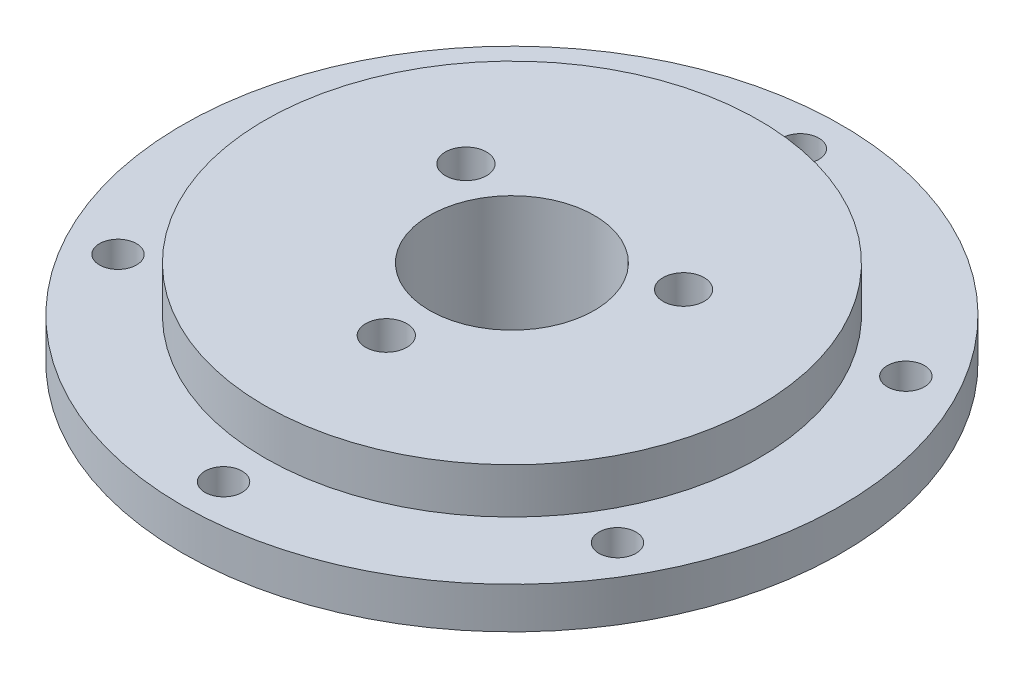
SolidWorks part; units mm, degrees
ref_plane "Front Plane" through (0, 0, 0) normal (0, 0, 1) x (1, 0, 0)
ref_plane "Top Plane" through (0, 0, 0) normal (0, 1, 0) x (1, 0, 0)
ref_plane "Right Plane" through (0, 0, 0) normal (1, 0, 0) x (0, 0, -1)
sketch "Sketch1" plane through (0, 0, 0) normal (0, 1, 0) x (1, 0, 0)
  circle A0 centre (0, 0) radius 40
  circle A1 centre (0, 0) radius 35 construction
  circle A2 centre (0, 35) radius 2.25
  circle A3 centre (0, 0) radius 35 construction
  circle A4 centre (30.3109, 17.5) radius 2.25
  circle A5 centre (0, 0) radius 35 construction
  circle A6 centre (30.3109, -17.5) radius 2.25
  circle A7 centre (0, 0) radius 35 construction
  circle A8 centre (0, -35) radius 2.25
  circle A9 centre (0, 0) radius 35 construction
  circle A10 centre (-30.3109, -17.5) radius 2.25
  circle A11 centre (0, 0) radius 35 construction
  circle A12 centre (-30.3109, 17.5) radius 2.25
  point P23 (0, 0)
  dimension "D1" = 80
  dimension "D2" = 70
  dimension "D3" = 4.5
  dimension "D4" = 6
extrude "Boss-Extrude1" add sketch "Sketch1" along normal blind 5
sketch "Sketch2" plane through (0, 5, 0) normal (0, 1, 0) x (1, 0, 0)
  circle A0 centre (0, 0) radius 30
  circle A1 centre (0, 0) radius 10
  circle A2 centre (0, 0) radius 15.25 construction
  circle A3 centre (0, -15.25) radius 2.5
  circle A4 centre (-13.2069, 7.625) radius 2.5
  circle A5 centre (13.2069, 7.625) radius 2.5
  point P7 (-7.3068, 15.25)
  point P8 (0, 0)
  point P14 (0, 0)
  dimension "D1" = 20
  dimension "D2" = 60
  dimension "D3" = 5
  dimension "D4" = 30.5
  dimension "D5" = 3
extrude "Boss-Extrude2" add sketch "Sketch2" along normal blind 5.5 and the other way offset from surface (10.5 mm away) 5.5 other way up to face at (0, 0, 40)
sketch "Sketch3" plane through (0, 10.5, 0) normal (0, 1, 0) x (1, 0, 0)
  circle A0 centre (0, -15.25) radius 2.5 construction
  circle A1 centre (13.2069, 7.625) radius 2.5 construction
  circle A3 centre (0, 0) radius 10 construction
  circle A4 centre (-13.2069, 7.625) radius 2.5 construction
  circle A5 centre (0, -15.25) radius 2.5
  circle A6 centre (13.2069, 7.625) radius 2.5
  circle A7 centre (0, 0) radius 10
  circle A8 centre (-13.2069, 7.625) radius 2.5
extrude "Cut-Extrude1" cut sketch "Sketch3" against normal through all
